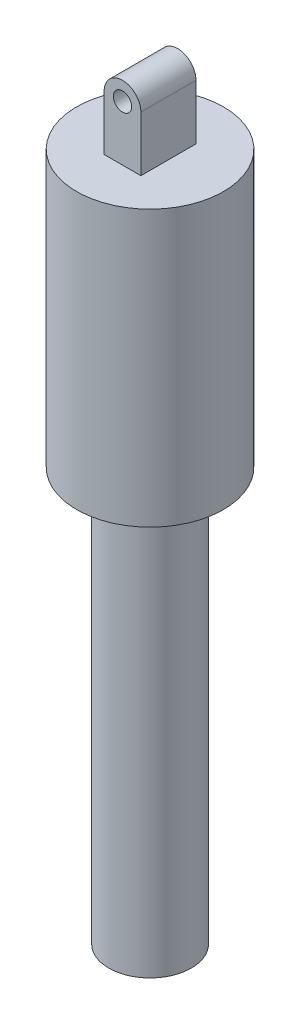
SolidWorks part; units mm, degrees
ref_plane "Plano frontal" through (0, 0, 0) normal (0, 0, 1) x (1, 0, 0)
ref_plane "Plano superior" through (0, 0, 0) normal (0, 1, 0) x (1, 0, 0)
ref_plane "Plano direito" through (0, 0, 0) normal (1, 0, 0) x (0, 0, -1)
sketch "Esboço1" plane through (0, 0, 0) normal (0, 0, 1) x (1, 0, 0)
  line L0 (0, 0) -> (0, 188.7706) construction
  line L1 (0, 0) -> (101.3657, 0) construction
  line L2 (0, 150) -> (40, 150)
  line L3 (40, 150) -> (40, 0)
  line L4 (22.5, 0) -> (40, 0)
  line L5 (0, 150) -> (0, 0)
  line L6 (22.5, 0) -> (22.5, -225)
  line L7 (22.5, -225) -> (9, -225)
  line L8 (9, -225) -> (9, 0)
  line L9 (9, 0) -> (0, 0)
  dimension "D1" = 45
  dimension "D2" = 225
  dimension "D3" = 150
  dimension "D4" = 80
  dimension "D5" = 18
revolve "Revolução1" add sketch "Esboço1" angle 360 about L0
sketch "Esboço2" plane through (0, 0, 0) normal (0, 0, 1) x (1, 0, 0)
  line L0 (0, 150) -> (0, 304.1007) construction
  line L1 (40, 150) -> (-40, 150) construction
  line L2 (10, 150) -> (10, 180)
  line L3 (10, 150) -> (-10, 150)
  line L4 (-10, 150) -> (-10, 180)
  arc A0 (10, 180) -> (-10, 180) centre (0, 180) ccw
  circle A1 centre (0, 180) radius 5
  dimension "D2" = 20
  dimension "D3" = 10
  dimension "D1" = 30
extrude "Ressalto-extrusão1" add sketch "Esboço2" along normal mid plane 30
